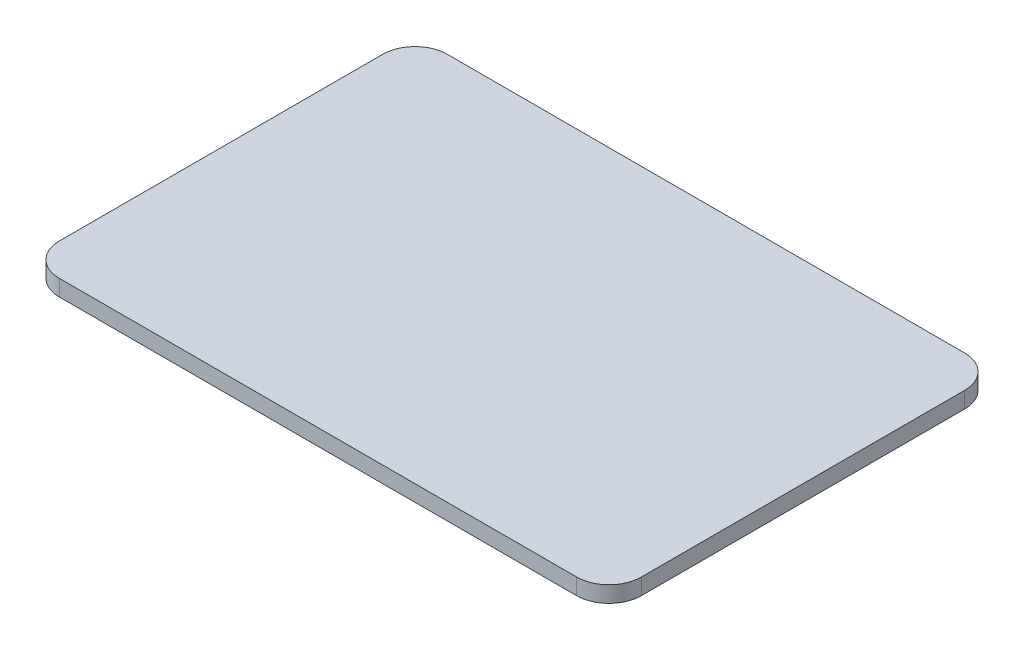
SolidWorks part; units mm, degrees
ref_plane "Front Plane" through (0, 0, 0) normal (0, 0, 1) x (1, 0, 0)
ref_plane "Top Plane" through (0, 0, 0) normal (0, 1, 0) x (1, 0, 0)
ref_plane "Right Plane" through (0, 0, 0) normal (1, 0, 0) x (0, 0, -1)
sketch "Sketch1" plane through (0, 0, 0) normal (0, 1, 0) x (1, 0, 0)
  line L1 (-90, -60) -> (90, -60)
  line L2 (-90, -60) -> (-90, 60)
  line L3 (-90, 60) -> (90, 60)
  line L4 (90, -60) -> (90, 60)
  line L5 (-90, -60) -> (90, 60) construction
  line L6 (-90, 60) -> (90, -60) construction
  point P0 (0, 0)
extrude "Boss-Extrude1" add sketch "Sketch1" along normal blind 5
fillet "Fillet1" radius 10 1 edges at (-90, 2.5, -60)
fillet "Fillet2" radius 10 1 edges at (-90, 2.5, 60)
fillet "Fillet3" radius 10 1 edges at (90, 2.5, 60)
fillet "Fillet4" radius 10 1 edges at (90, 2.5, -60)
